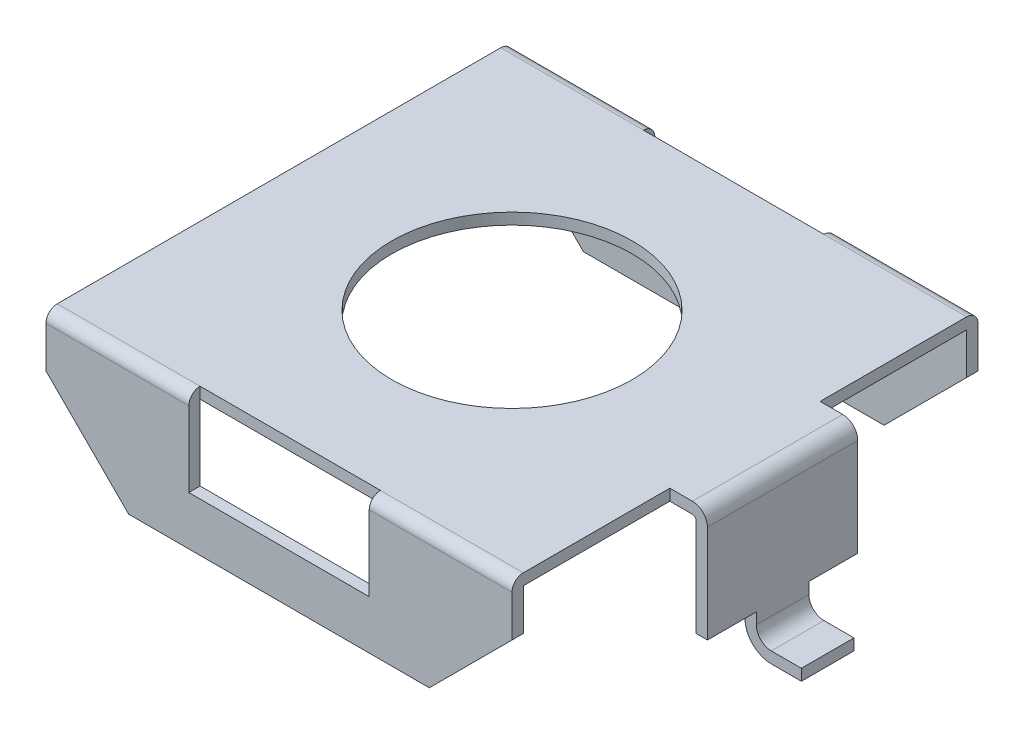
SolidWorks part; units mm, degrees
ref_plane "Front Plane" through (0, 0, 0) normal (0, 0, 1) x (1, 0, 0)
ref_plane "Top Plane" through (0, 0, 0) normal (0, 1, 0) x (1, 0, 0)
ref_plane "Right Plane" through (0, 0, 0) normal (1, 0, 0) x (0, 0, -1)
sketch "Sketch1" plane through (0, 0, 0) normal (1, 0, 0) x (0, 0, -1)
  line L0 (-3.1, 0.2) -> (-3.1, 2)
  line L1 (-3.1, 2) -> (3.1, 2)
  line L2 (3.1, 2) -> (3.1, 0.2)
  line L3 (3.41, 0) -> (-3.41, 0) construction
  line L4 (0, 0.99) -> (0, -0.99) construction
  dimension "D1" = 2
  dimension "D2" = 6.2
  dimension "D3" = 3.1
  dimension "D4" = 1.8
extrude "Extrude-Thin3" add sketch "Sketch1" along normal mid plane 6.2 thin
sketch "Sketch2" plane through (0, 0, 0) normal (0, 0, 1) x (1, 0, 0)
  line L1 (-1.2, 1.85) -> (1.2, 1.85)
  line L2 (-1.2, 1.85) -> (-1.2, 0.85)
  line L3 (-1.2, 0.85) -> (1.2, 0.85)
  line L4 (1.2, 1.85) -> (1.2, 0.85)
  line L5 (-3.1, 1.3) -> (-2, 0.2)
  line L6 (3.1, 0.2) -> (3.1, 1.3)
  line L7 (3.1, 0.2) -> (-3.1, 0.2) construction
  line L8 (-2, 0.2) -> (-3.1, 0.2)
  line L9 (-3.1, 0.2) -> (-3.1, 1.3)
  line L10 (-3.1, 0.2) -> (-3.1, 2) construction
  line L11 (3.1, 1.3) -> (2, 0.2)
  line L12 (3.1, 0.2) -> (3.1, 2) construction
  line L13 (2, 0.2) -> (3.1, 0.2)
  line L14 (0, -0.99) -> (0, 0.99) construction
  dimension "D1" = 4
  dimension "D2" = 2
  dimension "D3" = 45
  dimension "D4" = 45
  dimension "D5" = 2.4
  dimension "D6" = 1.2
extrude "Cut-Extrude1" cut sketch "Sketch2" against normal through all and the other way through all
sketch "Sketch3" plane through (0, 2, 0) normal (0, 1, 0) x (1, 0, 0)
  line L1 (-1.2, 3.1) -> (1.2, 3.1)
  line L2 (-1.2, 3.1) -> (-1.2, 2.95)
  line L3 (-1.2, 2.95) -> (1.2, 2.95)
  line L4 (1.2, 3.1) -> (1.2, 2.95)
  line L5 (-1.2, -3.1) -> (1.2, -3.1)
  line L6 (-1.2, -3.1) -> (-1.2, -2.95)
  line L7 (-1.2, -2.95) -> (1.2, -2.95)
  line L8 (1.2, -3.1) -> (1.2, -2.95)
extrude "Cut-Extrude2" cut sketch "Sketch3" against normal blind 1
fillet "Fillet1" radius 0.15 4 edges at (-2.15, 2, -3.1) (2.15, 2, -3.1) (-2.15, 2, 3.1) (2.15, 2, 3.1)
sketch "Sketch4" plane through (0, 2, 0) normal (0, 1, 0) x (1, 0, 0)
  circle A0 centre (0, 0) radius 1.6
  dimension "D1" = 3.2
extrude "Cut-Extrude3" cut sketch "Sketch4" against normal blind 1
sketch "Sketch5" plane through (0, 0, 0) normal (0, 0, 1) x (1, 0, 0)
  line L0 (3.1, 2) -> (3.4, 2)
  line L1 (3.6, 1.8) -> (3.6, 0.35)
  line L2 (3.8, 0.15) -> (4.2, 0.15)
  line L3 (3.41, 0) -> (-3.41, 0) construction
  line L4 (0, -0.99) -> (0, 0.99) construction
  line L5 (3.1, 1.3) -> (3.1, 1.85) construction
  arc A0 (3.6, 0.35) -> (3.8, 0.15) centre (3.8, 0.35) ccw
  arc A1 (3.4, 2) -> (3.6, 1.8) centre (3.4, 1.8) cw
  point P9 (3.1, 1.575)
  dimension "D5" = 0.2
  dimension "D1" = 0.15
  dimension "D2" = 3.6
  dimension "D3" = 0.5
  dimension "D4" = 4.2
extrude "Extrude-Thin4" add sketch "Sketch5" along normal mid plane 2 thin
sketch "Sketch6" plane through (0, 0, 0) normal (0, -1, 0) x (1, 0, 0)
  line L1 (4.2, 1) -> (3.2, 1)
  line L2 (4.2, 1) -> (4.2, 0.35)
  line L3 (4.2, 0.35) -> (3.2, 0.35)
  line L4 (3.2, 1) -> (3.2, 0.35)
  line L5 (4.2, -1) -> (3.2, -1)
  line L6 (4.2, -1) -> (4.2, -0.35)
  line L7 (4.2, -0.35) -> (3.2, -0.35)
  line L8 (3.2, -1) -> (3.2, -0.35)
  dimension "D1" = 1
  dimension "D2" = 0.7
extrude "Cut-Extrude4" cut sketch "Sketch6" against normal blind 0.5
